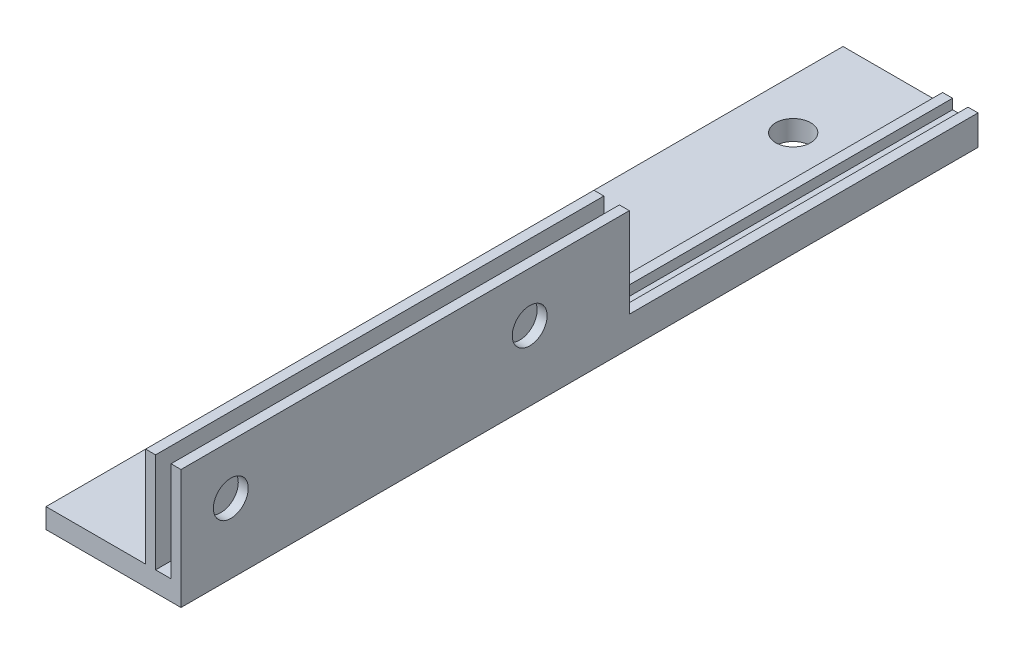
SolidWorks part; units mm, degrees
ref_plane "Front Plane" through (0, 0, 0) normal (0, 0, 1) x (1, 0, 0)
ref_plane "Top Plane" through (0, 0, 0) normal (0, 1, 0) x (1, 0, 0)
ref_plane "Right Plane" through (0, 0, 0) normal (1, 0, 0) x (0, 0, -1)
sketch "Sketch1" plane through (0, 0, 0) normal (0, 0, 1) x (1, 0, 0)
  line L0 (0, 0) -> (0, 2)
  line L3 (13.55, 0) -> (0, 0)
  line L4 (13.55, 0) -> (13.55, 12)
  line L5 (12.55, 12) -> (12.55, 2)
  line L6 (12.55, 2) -> (11, 2)
  line L7 (11, 2) -> (11, 12)
  line L8 (13.55, 12) -> (12.55, 12)
  line L9 (0, 2) -> (10, 2)
  line L10 (10, 2) -> (10, 12)
  line L11 (10, 12) -> (11, 12)
  dimension "D1" = 2
  dimension "D2" = 12
  dimension "D3" = 10
  dimension "D4" = 2
  dimension "D5" = 1.55
  dimension "D6" = 1
  dimension "D7" = 1
extrude "Boss-Extrude1" add sketch "Sketch1" along normal blind 45
sketch "Sketch4" plane through (0, 0, 0) normal (0, 0, 1) x (1, 0, 0)
  line L0 (0, 2) -> (0, 0)
  line L1 (0, 0) -> (13.55, 0)
  line L2 (13.55, 0) -> (13.55, 3)
  line L3 (13.55, 0) -> (13.55, 12) construction
  line L4 (13.55, 3) -> (12.55, 3)
  line L5 (12.55, 12) -> (12.55, 2) construction
  line L6 (12.55, 3) -> (12.55, 2)
  line L7 (12.55, 2) -> (11, 2)
  line L8 (11, 2) -> (11, 3)
  line L9 (11, 2) -> (11, 12) construction
  line L10 (11, 3) -> (10, 3)
  line L11 (10, 12) -> (10, 2) construction
  line L12 (10, 3) -> (10, 2)
  line L13 (10, 2) -> (0, 2)
  dimension "D1" = 1
extrude "Boss-Extrude2" add sketch "Sketch4" against normal blind 35
sketch "Sketch2" plane through (10, 0, 0) normal (-1, 0, 0) x (0, 0, 1)
  line L0 (45, 12) -> (45, 2) construction
  line L7 (45, 2) -> (-35, 2) construction
  circle A0 centre (40, 7) radius 1.75
  circle A1 centre (10, 7) radius 1.75
  dimension "D1" = 3.5
  dimension "D3" = 3.5
  dimension "D2" = 5
  dimension "D4" = 5
  dimension "D5" = 5
  dimension "D6" = 30
extrude "Cut-Extrude1" cut sketch "Sketch2" against normal through all
sketch "Sketch3" plane through (0, 2, 0) normal (0, 1, 0) x (1, 0, 0)
  line L0 (5, 35) -> (5, 25) construction
  line L1 (10, 35) -> (0, 35) construction
  line L2 (5, 25) -> (5, -35) construction
  line L3 (5, -35) -> (5, -45) construction
  line L5 (10, -45) -> (0, -45) construction
  circle A0 centre (5, 25) radius 1.75
  circle A1 centre (5, -35) radius 1.75
  dimension "D1" = 3.5
  dimension "D2" = 3.5
  dimension "D3" = 10
extrude "Cut-Extrude2" cut sketch "Sketch3" against normal up to next
